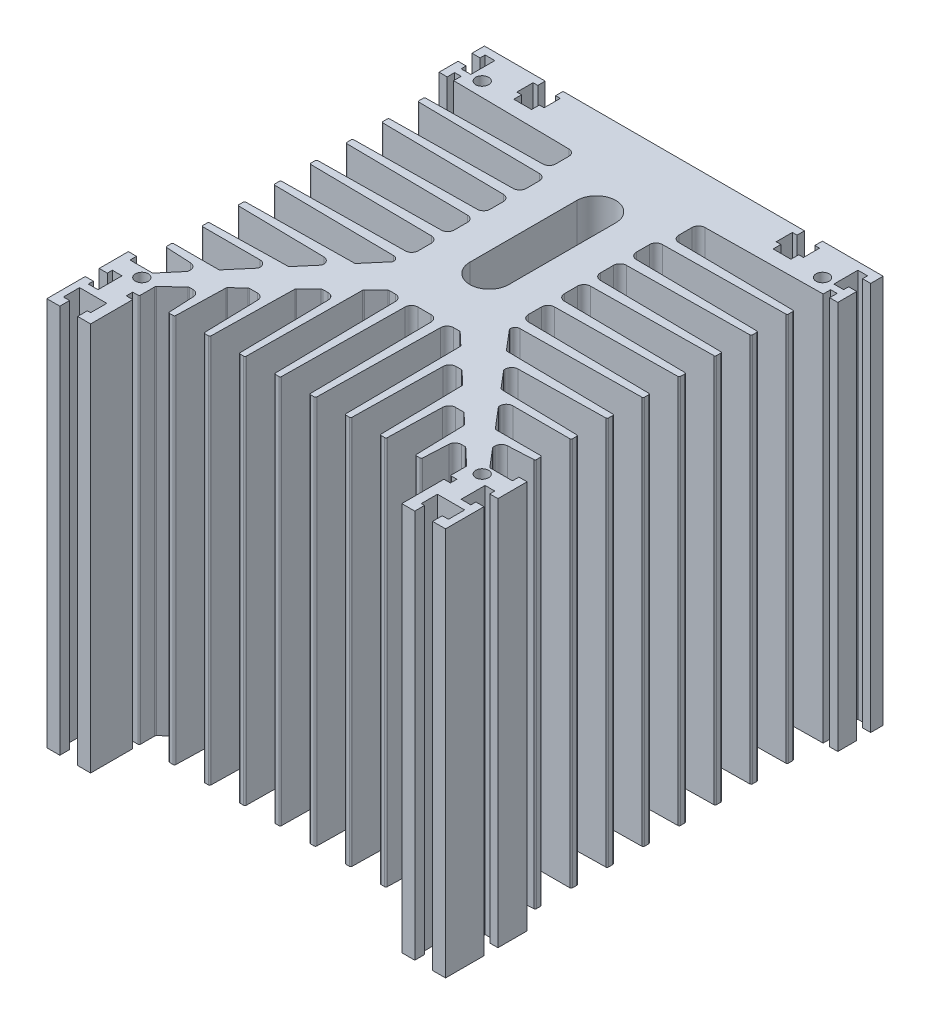
SolidWorks part; units mm, degrees
ref_plane "Alzado" through (0, 0, 0) normal (0, 0, 1) x (1, 0, 0)
ref_plane "Planta" through (0, 0, 0) normal (0, 1, 0) x (1, 0, 0)
ref_plane "Vista lateral" through (0, 0, 0) normal (1, 0, 0) x (0, 0, -1)
sketch "Croquis1" plane through (0, 0, 0) normal (0, 1, 0) x (1, 0, 0)
  line L0 (0, 0) -> (0, 30.5493) construction
  line L1 (-57.5, -11.85) -> (-57.5, -8.85)
  line L2 (-57.5, -8.85) -> (-59.4, -8.85)
  line L3 (-59.4, -8.85) -> (-59.4, -3.85)
  line L4 (-59.4, -3.85) -> (-51, -3.85)
  line L5 (-51, -3.85) -> (-51, -8.85)
  line L6 (-51, -8.85) -> (-52, -8.85)
  line L7 (-52, -8.85) -> (-52, -11.85)
  line L8 (-52, -11.85) -> (-48, -11.85)
  line L9 (-48, -11.85) -> (-48, 1.15)
  line L13 (-57.5, -11.85) -> (-61.5, -11.85)
  line L14 (-61.5, -11.85) -> (-61.5, 0)
  line L15 (-61.5, 0) -> (-59, 0)
  line L16 (-59, 0) -> (-59, -1.55)
  line L17 (-59, -1.55) -> (-56, -1.55)
  line L18 (-56, -1.55) -> (-56, 5.85)
  line L19 (-56, 5.85) -> (-59, 5.85)
  line L20 (-59, 5.85) -> (-59, 4.3)
  line L21 (-59, 4.3) -> (-61.5, 4.3)
  line L22 (-61.5, 4.3) -> (-61.5, 13.3)
  line L23 (-61.5, 13.3) -> (-59, 13.3)
  line L24 (-59, 13.3) -> (-59, 11.3)
  line L25 (-59, 11.3) -> (-57, 11.3)
  line L26 (-48, 1.15) -> (-50, 1.15)
  line L27 (-50, 1.15) -> (-50, 3.15)
  line L28 (-50, 3.15) -> (50, 3.15)
  line L29 (-61.5, 123.15) -> (-189.2921, 123.15) construction
  line L30 (-61.5, 123.15) -> (-61.5, 119.3)
  line L31 (-61.5, 119.3) -> (-59, 119.3)
  line L32 (-59, 119.3) -> (-59, 120.85)
  line L33 (-59, 120.85) -> (-56, 120.85)
  line L34 (-56, 120.85) -> (-56, 113.45)
  line L35 (-56, 113.45) -> (-59, 113.45)
  line L36 (-59, 113.45) -> (-59, 115)
  line L37 (-59, 115) -> (-61.5, 115)
  line L38 (-61.5, 115) -> (-61.5, 109.15)
  line L39 (-61.5, 109.15) -> (-59, 109.15)
  line L40 (-59, 109.15) -> (-59, 111.45)
  line L41 (-59, 111.45) -> (-57, 111.45)
  line L42 (-57, 111.45) -> (-57, 11.3)
  line L43 (37.25, 123.15) -> (-1, 123.15)
  line L44 (37.25, 120.85) -> (37.25, 123.15)
  line L45 (-61.5, 123.15) -> (-42.75, 123.15)
  line L46 (35.8, 120.85) -> (37.25, 120.85)
  line L47 (-42.75, 123.15) -> (-42.75, 120.85)
  line L48 (-42.75, 120.85) -> (-44.2, 120.85)
  line L49 (-44.2, 120.85) -> (-44.2, 115.85)
  line L50 (-44.2, 115.85) -> (-42.75, 115.85)
  line L51 (-42.75, 115.85) -> (-42.75, 113.45)
  line L52 (-42.75, 113.45) -> (-37.25, 113.45)
  line L53 (-37.25, 113.45) -> (-37.25, 115.85)
  line L54 (-37.25, 115.85) -> (-35.8, 115.85)
  line L55 (-35.8, 115.85) -> (-35.8, 120.85)
  line L56 (-35.8, 120.85) -> (-37.25, 120.85)
  line L57 (-37.25, 120.85) -> (-37.25, 123.15)
  line L58 (-37.25, 123.15) -> (1, 123.15)
  line L59 (35.8, 115.85) -> (35.8, 120.85)
  line L60 (37.25, 115.85) -> (35.8, 115.85)
  line L61 (37.25, 113.45) -> (37.25, 115.85)
  line L62 (42.75, 113.45) -> (37.25, 113.45)
  line L63 (42.75, 115.85) -> (42.75, 113.45)
  line L64 (44.2, 115.85) -> (42.75, 115.85)
  line L65 (44.2, 120.85) -> (44.2, 115.85)
  line L66 (42.75, 120.85) -> (44.2, 120.85)
  line L67 (42.75, 123.15) -> (42.75, 120.85)
  line L68 (61.5, 123.15) -> (42.75, 123.15)
  line L69 (57, 111.45) -> (57, 11.3)
  line L70 (59, 111.45) -> (57, 111.45)
  line L71 (59, 109.15) -> (59, 111.45)
  line L72 (61.5, 109.15) -> (59, 109.15)
  line L73 (61.5, 115) -> (61.5, 109.15)
  line L74 (59, 115) -> (61.5, 115)
  line L75 (59, 113.45) -> (59, 115)
  line L76 (56, 113.45) -> (59, 113.45)
  line L77 (56, 120.85) -> (56, 113.45)
  line L78 (59, 120.85) -> (56, 120.85)
  line L79 (59, 119.3) -> (59, 120.85)
  line L80 (61.5, 119.3) -> (59, 119.3)
  line L81 (61.5, 123.15) -> (61.5, 119.3)
  line L82 (50, 1.15) -> (50, 3.15)
  line L83 (48, 1.15) -> (50, 1.15)
  line L84 (59, 11.3) -> (57, 11.3)
  line L85 (59, 13.3) -> (59, 11.3)
  line L86 (61.5, 13.3) -> (59, 13.3)
  line L87 (61.5, 4.3) -> (61.5, 13.3)
  line L88 (59, 4.3) -> (61.5, 4.3)
  line L89 (59, 5.85) -> (59, 4.3)
  line L90 (56, 5.85) -> (59, 5.85)
  line L91 (56, -1.55) -> (56, 5.85)
  line L92 (59, -1.55) -> (56, -1.55)
  line L93 (59, 0) -> (59, -1.55)
  line L94 (61.5, 0) -> (59, 0)
  line L95 (61.5, -11.85) -> (61.5, 0)
  line L96 (57.5, -11.85) -> (61.5, -11.85)
  line L97 (48, -11.85) -> (48, 1.15)
  line L98 (52, -11.85) -> (48, -11.85)
  line L99 (52, -8.85) -> (52, -11.85)
  line L100 (51, -8.85) -> (52, -8.85)
  line L101 (51, -3.85) -> (51, -8.85)
  line L102 (59.4, -3.85) -> (51, -3.85)
  line L103 (59.4, -8.85) -> (59.4, -3.85)
  line L104 (57.5, -8.85) -> (59.4, -8.85)
  line L105 (57.5, -11.85) -> (57.5, -8.85)
  point P13 (-52, -10.35)
  point P62 (-37.25, 122)
  point P91 (0, 3.15)
  point P115 (-40, 113.45)
  dimension "D1" = 5.5
  dimension "D2" = 4
  dimension "D3" = 13
  dimension "D4" = 8.4
  dimension "D5" = 1
  dimension "D6" = 5
  dimension "D7" = 96
  dimension "D8" = 3
  dimension "D9" = 11.85
  dimension "D10" = 2.5
  dimension "D11" = 3
  dimension "D12" = 4.3
  dimension "D13" = 7.4
  dimension "D14" = 9
  dimension "D15" = 135
  dimension "D16" = 40
  dimension "D17" = 2
  dimension "D18" = 62.5
  dimension "D20" = 7.4
  dimension "D21" = 4.3
  dimension "D22" = 3.85
  dimension "D23" = 2.5
  dimension "D24" = 14
  dimension "D25" = 2
  dimension "D26" = 2
  dimension "D28" = 8.4
  dimension "D29" = 5.5
  dimension "D30" = 5
extrude "Saliente-Extruir1" add sketch "Croquis1" along normal blind 120 contours L105 L96 L95 L94 L93 L92 L91 L90 L89 L88 L87 L86 L85 L84 L69 L70 L71 L72 L73 L74 L75 L76 L77 L78 L79 L80 L81 L68 L67 L66 L65 L64 L63 L62 L61 L60 L59 L46 L44 L43 L58 L57 L56 L55 L54 L53 L52 L51 L50 L49
sketch "Croquis2" plane through (0, 120, 0) normal (0, 1, 0) x (1, 0, 0)
  line L0 (0, 3.15) -> (0, 43.15) construction
  line L1 (-50, 3.15) -> (50, 3.15) construction
  line L2 (-2.0248, 43.15) -> (2.0248, 43.15)
  line L3 (-48, 3.15) -> (-48, 8.15)
  line L4 (-48, -11.85) -> (-48, 1.15) construction
  line L5 (-11, 43.15) -> (11, 43.15) construction
  line L6 (-48, 8.15) -> (-11, 43.15) construction
  line L7 (48, 8.15) -> (11, 43.15) construction
  line L8 (48, 3.15) -> (48, 7.9347)
  line L9 (-4.5, 3.15) -> (4.5, 3.15)
  line L10 (-4.0247, 41.175) -> (-4.5, 3.15)
  line L11 (4.0247, 41.175) -> (4.5, 3.15)
  line L12 (6.375, 3.15) -> (15.375, 3.15)
  line L13 (10.875, 3.15) -> (11, 43.15) construction
  line L15 (6.9692, 41.1812) -> (6.375, 3.15)
  line L16 (15.0375, 39.1201) -> (15.375, 3.15)
  line L17 (11.1446, 43.0132) -> (14.8812, 39.4786)
  line L18 (8.969, 43.15) -> (10.801, 43.15)
  line L19 (17.25, 3.15) -> (26.25, 3.15)
  line L20 (21.75, 3.15) -> (21.75, 33.15) construction
  line L21 (21.3724, 33.15) -> (19.7169, 33.15)
  line L22 (17.7172, 31.1833) -> (17.25, 3.15)
  line L24 (25.7845, 28.9584) -> (26.25, 3.15)
  line L25 (21.716, 33.0132) -> (25.6281, 29.3126)
  line L26 (28.125, 3.15) -> (37.125, 3.15)
  line L27 (48, 3.15) -> (39, 3.15)
  line L28 (32.625, 3.15) -> (32.625, 22.15) construction
  line L29 (32.625, 22.15) -> (30.5731, 22.15)
  line L30 (28.5738, 20.2026) -> (28.125, 3.15)
  line L31 (32.625, 22.15) -> (33.001, 22.15)
  line L32 (36.7179, 18.62) -> (37.125, 3.15)
  line L33 (33.3446, 22.0132) -> (36.5617, 18.97)
  line L34 (43.5, 3.15) -> (43.5, 13.15) construction
  line L35 (42.5153, 13.15) -> (41.4025, 13.15)
  line L36 (39, 3.15) -> (39.405, 11.2499)
  line L37 (42.8589, 13.0132) -> (47.8436, 8.2979)
  line L38 (-43.5, 3.15) -> (-43.5, 13.15) construction
  line L39 (-32.625, 3.15) -> (-32.625, 22.15) construction
  line L40 (-21.75, 3.15) -> (-21.75, 33.15) construction
  line L41 (-10.875, 3.15) -> (-11, 43.15) construction
  line L42 (-48, 8.15) -> (-11, 43.15) construction
  line L43 (-42.8589, 13.0132) -> (-47.8436, 8.2979)
  line L44 (-39, 3.15) -> (-39.405, 11.2499)
  line L45 (-42.5153, 13.15) -> (-41.4025, 13.15)
  line L46 (-33.3446, 22.0132) -> (-36.5617, 18.97)
  line L47 (-36.7179, 18.62) -> (-37.125, 3.15)
  line L48 (-32.625, 22.15) -> (-33.001, 22.15)
  line L49 (-28.5738, 20.2026) -> (-28.125, 3.15)
  line L50 (-32.625, 22.15) -> (-30.5731, 22.15)
  line L51 (-48, 3.15) -> (-39, 3.15)
  line L52 (-28.125, 3.15) -> (-37.125, 3.15)
  line L53 (-21.716, 33.0132) -> (-25.6281, 29.3126)
  line L54 (-25.7845, 28.9584) -> (-26.25, 3.15)
  line L55 (-17.7172, 31.1833) -> (-17.25, 3.15)
  line L56 (-21.3724, 33.15) -> (-19.7169, 33.15)
  line L57 (-17.25, 3.15) -> (-26.25, 3.15)
  line L58 (-8.969, 43.15) -> (-10.801, 43.15)
  line L59 (-11.1446, 43.0132) -> (-14.8812, 39.4786)
  line L60 (-15.0375, 39.1201) -> (-15.375, 3.15)
  line L61 (-6.9692, 41.1812) -> (-6.375, 3.15)
  line L62 (-6.375, 3.15) -> (-15.375, 3.15)
  line L63 (-48, 3.15) -> (-48, 7.9347)
  arc A0 (41.4025, 13.15) -> (39.405, 11.2499) centre (41.4025, 11.15) ccw
  arc A1 (30.5731, 22.15) -> (28.5738, 20.2026) centre (30.5731, 20.15) ccw
  arc A2 (19.7169, 33.15) -> (17.7172, 31.1833) centre (19.7169, 31.15) ccw
  arc A3 (8.969, 43.15) -> (6.9692, 41.1812) centre (8.969, 41.15) ccw
  arc A4 (2.0248, 43.15) -> (4.0247, 41.175) centre (2.0248, 41.15) cw
  arc A5 (-2.0248, 43.15) -> (-4.0247, 41.175) centre (-2.0248, 41.15) ccw
  arc A6 (47.8436, 8.2979) -> (48, 7.9347) centre (47.5, 7.9347) cw
  arc A7 (42.8589, 13.0132) -> (42.5153, 13.15) centre (42.5153, 12.65) ccw
  arc A8 (36.5617, 18.97) -> (36.7179, 18.62) centre (36.2181, 18.6068) cw
  arc A9 (33.3446, 22.0132) -> (33.001, 22.15) centre (33.001, 21.65) ccw
  arc A10 (25.6281, 29.3126) -> (25.7845, 28.9584) centre (25.2845, 28.9493) cw
  arc A11 (21.716, 33.0132) -> (21.3724, 33.15) centre (21.3724, 32.65) ccw
  arc A12 (14.8812, 39.4786) -> (15.0375, 39.1201) centre (14.5376, 39.1154) cw
  arc A13 (11.1446, 43.0132) -> (10.801, 43.15) centre (10.801, 42.65) ccw
  arc A14 (-11.1446, 43.0132) -> (-10.801, 43.15) centre (-10.801, 42.65) cw
  arc A15 (-14.8812, 39.4786) -> (-15.0375, 39.1201) centre (-14.5376, 39.1154) ccw
  arc A16 (-21.716, 33.0132) -> (-21.3724, 33.15) centre (-21.3724, 32.65) cw
  arc A17 (-25.6281, 29.3126) -> (-25.7845, 28.9584) centre (-25.2845, 28.9493) ccw
  arc A18 (-33.3446, 22.0132) -> (-33.001, 22.15) centre (-33.001, 21.65) cw
  arc A19 (-36.5617, 18.97) -> (-36.7179, 18.62) centre (-36.2181, 18.6068) ccw
  arc A20 (-42.8589, 13.0132) -> (-42.5153, 13.15) centre (-42.5153, 12.65) cw
  arc A21 (-47.8436, 8.2979) -> (-48, 7.9347) centre (-47.5, 7.9347) ccw
  arc A22 (-8.969, 43.15) -> (-6.9692, 41.1812) centre (-8.969, 41.15) cw
  arc A23 (-19.7169, 33.15) -> (-17.7172, 31.1833) centre (-19.7169, 31.15) cw
  arc A24 (-30.5731, 22.15) -> (-28.5738, 20.2026) centre (-30.5731, 20.15) cw
  arc A25 (-41.4025, 13.15) -> (-39.405, 11.2499) centre (-41.4025, 11.15) cw
  point P8 (0, 43.15)
  point P14 (0, 43.15)
  point P20 (0, 3.15)
  point P26 (11, 43.15)
  point P30 (21.75, 3.15)
  point P48 (39.5, 13.15)
  point P51 (28.625, 22.15)
  point P54 (17.75, 33.15)
  point P57 (7, 43.15)
  point P60 (4, 43.15)
  point P63 (-4, 43.15)
  point P69 (42.7143, 13.15)
  point P72 (36.7124, 18.8274)
  point P75 (33.2, 22.15)
  point P78 (25.7807, 29.1683)
  point P81 (21.5714, 33.15)
  point P84 (15.0355, 39.3326)
  point P138 (-15.0355, 39.3326)
  point P139 (-21.5714, 33.15)
  point P140 (-25.7807, 29.1683)
  point P141 (-33.2, 22.15)
  point P142 (-36.7124, 18.8274)
  point P143 (-42.7143, 13.15)
  point P144 (-7, 43.15)
  point P145 (-17.75, 33.15)
  point P146 (-28.625, 22.15)
  point P147 (-39.5, 13.15)
  dimension "D24" = 2
  dimension "D25" = 0.5
  dimension "D1" = 40
  dimension "D2" = 8
  dimension "D3" = 5
  dimension "D4" = 22
  dimension "D5" = 9
  dimension "D6" = 1.875
  dimension "D7" = 9
  dimension "D8" = 7.9994
  dimension "D9" = 4
  dimension "D10" = 1.875
  dimension "D11" = 30
  dimension "D12" = 4
  dimension "D13" = 8.0959
  dimension "D14" = 9
  dimension "D15" = 1.875
  dimension "D16" = 9
  dimension "D17" = 19
  dimension "D18" = 4
  dimension "D19" = 8.0874
  dimension "D20" = 8
  dimension "D21" = 10
  dimension "D22" = 4
  dimension "D23" = 4
extrude "Cortar-Extruir1" cut sketch "Croquis2" against normal blind 120 contours A25 L45 A20 L43 A21 L3 L51 L44 | A24 L50 L48 A18 L46 A19 L47 L52 L49 | A23 L56 A16 L53 A17 L54 L57 L55 | A22 L58 A14 L59 A15 L60 L62 L61 | L2 A5 L10 L9 L11 A4 | L17 A13 L18 A3 L15 L12 L16 A12 | L25 A11 L21 A2 L22 L19 L24 A10 | L33 A9 L31 L29 A1 L30 L26 L32 A8 | L37 A7 L35 A0 L36 L27 L8 A6
fillet "Redondeo1" radius 0.4 18 edges at (48, 60, -3.15) (-48, 60, -3.15) (39, 60, -3.15) (37.125, 60, -3.15) (28.125, 60, -3.15) (26.25, 60, -3.15) (17.25, 60, -3.15) (15.375, 60, -3.15) (6.375, 60, -3.15) (4.5, 60, -3.15) (-4.5, 60, -3.15) (-6.375, 60, -3.15) (-15.375, 60, -3.15) (-17.25, 60, -3.15) (-26.25, 60, -3.15) (-28.125, 60, -3.15) (-37.125, 60, -3.15) (-39, 60, -3.15)
sketch "Croquis3" plane through (0, 120, 0) normal (0, 1, 0) x (1, 0, 0)
  line L0 (-57, 109.15) -> (-19, 109.15) construction
  line L1 (-57, 111.45) -> (-57, 11.3) construction
  line L2 (-61.5, 109.15) -> (-59, 109.15) construction
  line L3 (-57, 109.15) -> (-57, 100.15)
  line L4 (-57, 104.65) -> (-19, 104.65) construction
  line L5 (-19, 102.6239) -> (-19, 106.6761)
  line L6 (-57, 109.15) -> (-20.9737, 108.676)
  line L7 (-57, 100.15) -> (-20.9737, 100.624)
  line L8 (-57, 98.0438) -> (-57, 89.0438)
  line L9 (-57, 93.5438) -> (-17, 93.5438) construction
  line L10 (-17, 91.5189) -> (-17, 95.5686)
  line L11 (-57, 98.0438) -> (-18.975, 97.5684)
  line L12 (-57, 89.0438) -> (-18.975, 89.5191)
  line L13 (-57, 86.9375) -> (-57, 77.9375)
  line L14 (-57, 82.4375) -> (-17, 82.4375) construction
  line L15 (-17, 80.4127) -> (-17, 84.4623)
  line L16 (-18.975, 86.4622) -> (-57, 86.9375)
  line L17 (-57, 77.9375) -> (-18.975, 78.4128)
  line L18 (-57, 75.8313) -> (-57, 66.8313)
  line L19 (-57, 71.3313) -> (-17, 71.3313) construction
  line L20 (-17, 69.3064) -> (-17, 73.3561)
  line L21 (-57, 75.8313) -> (-18.975, 75.3559)
  line L22 (-57, 66.8313) -> (-18.975, 67.3066)
  line L23 (-57, 64.725) -> (-57, 55.725)
  line L24 (-57, 60.225) -> (-17, 60.225) construction
  line L25 (-17, 58.2002) -> (-17, 62.2498)
  line L26 (-18.975, 64.2497) -> (-57, 64.725)
  line L27 (-57, 55.725) -> (-18.975, 56.2003)
  line L28 (-57, 11.3) -> (-52.2315, 11.3)
  line L29 (-17, 97.5438) -> (-17, 52.5438) construction
  line L30 (-56, 117.15) -> (-61.4392, 117.15) construction
  line L31 (-57, 31.4063) -> (-57, 22.4063)
  line L32 (-56, 120.85) -> (-56, 113.45) construction
  line L33 (-56, 2.15) -> (-61.4392, 2.15) construction
  line L34 (-57, 26.9063) -> (-37, 26.9063) construction
  line L35 (-37, 29.1595) -> (-37, 29.4063)
  line L36 (-57, 31.4063) -> (-39, 31.4063)
  line L37 (-56, -1.55) -> (-56, 5.85) construction
  line L38 (-57, 53.6188) -> (-57, 44.6188)
  line L39 (-57, 49.1188) -> (-18, 49.1188) construction
  line L40 (-18, 51.5489) -> (-18, 51.6379)
  line L41 (-57, 53.6188) -> (-19.4808, 53.1377)
  line L42 (-17, 52.5438) -> (-52, 11.3) construction
  line L44 (-23.5556, 45.0833) -> (-57, 44.6188)
  line L45 (-18.1188, 51.2254) -> (-23.1814, 45.2597)
  line L46 (-57, 42.5125) -> (-57, 33.5125)
  line L47 (-57, 38.0125) -> (-29.3314, 38.0125) construction
  line L48 (-28, 39.765) -> (-28, 40.0467)
  line L49 (-29.9655, 42.0464) -> (-57, 42.5125)
  line L51 (-57, 33.5125) -> (-32.9511, 34.0079)
  line L52 (-28.1188, 39.4415) -> (-32.5801, 34.1842)
  line L53 (-57, 22.4063) -> (-42.8066, 22.4063)
  line L54 (-42.4253, 22.5827) -> (-37.1188, 28.8359)
  line L55 (-57, 11.3) -> (-57, 20.3)
  line L56 (-57, 15.8) -> (-47, 15.8) construction
  line L57 (-57, 20.3) -> (-48.9001, 19.895)
  line L58 (-47, 17.8975) -> (-47, 17.3755)
  line L59 (-51.8502, 11.4765) -> (-47.1188, 17.052)
  line L60 (0, 0) -> (0, 43.15) construction
  line L61 (-2.0248, 43.15) -> (2.0248, 43.15) construction
  line L62 (57, 15.8) -> (47, 15.8) construction
  line L63 (57, 38.0125) -> (29.3314, 38.0125) construction
  line L64 (17, 52.5438) -> (52, 11.3) construction
  line L65 (57, 49.1188) -> (18, 49.1188) construction
  line L66 (57, 26.9063) -> (37, 26.9063) construction
  line L67 (56, 2.15) -> (61.4392, 2.15) construction
  line L68 (56, 117.15) -> (61.4392, 117.15) construction
  line L69 (17, 97.5438) -> (17, 52.5438) construction
  line L70 (57, 60.225) -> (17, 60.225) construction
  line L71 (57, 71.3313) -> (17, 71.3313) construction
  line L72 (57, 82.4375) -> (17, 82.4375) construction
  line L73 (57, 93.5438) -> (17, 93.5438) construction
  line L74 (57, 104.65) -> (19, 104.65) construction
  line L75 (57, 109.15) -> (19, 109.15) construction
  line L76 (51.8502, 11.4765) -> (47.1188, 17.052)
  line L77 (47, 17.8975) -> (47, 17.3755)
  line L78 (57, 20.3) -> (48.9001, 19.895)
  line L79 (57, 11.3) -> (57, 20.3)
  line L80 (42.4253, 22.5827) -> (37.1188, 28.8359)
  line L81 (57, 22.4063) -> (42.8066, 22.4063)
  line L82 (28.1188, 39.4415) -> (32.5801, 34.1842)
  line L83 (57, 33.5125) -> (32.9511, 34.0079)
  line L84 (29.9655, 42.0464) -> (57, 42.5125)
  line L85 (28, 39.765) -> (28, 40.0467)
  line L86 (57, 42.5125) -> (57, 33.5125)
  line L87 (18.1188, 51.2254) -> (23.1814, 45.2597)
  line L88 (23.5556, 45.0833) -> (57, 44.6188)
  line L89 (57, 53.6188) -> (19.4808, 53.1377)
  line L90 (18, 51.5489) -> (18, 51.6379)
  line L91 (57, 53.6188) -> (57, 44.6188)
  line L92 (57, 31.4063) -> (39, 31.4063)
  line L93 (37, 29.1595) -> (37, 29.4063)
  line L94 (57, 31.4063) -> (57, 22.4063)
  line L95 (57, 11.3) -> (52.2315, 11.3)
  line L96 (57, 55.725) -> (18.975, 56.2003)
  line L97 (18.975, 64.2497) -> (57, 64.725)
  line L98 (17, 58.2002) -> (17, 62.2498)
  line L99 (57, 64.725) -> (57, 55.725)
  line L100 (57, 66.8313) -> (18.975, 67.3066)
  line L101 (57, 75.8313) -> (18.975, 75.3559)
  line L102 (17, 69.3064) -> (17, 73.3561)
  line L103 (57, 75.8313) -> (57, 66.8313)
  line L104 (57, 77.9375) -> (18.975, 78.4128)
  line L105 (18.975, 86.4622) -> (57, 86.9375)
  line L106 (17, 80.4127) -> (17, 84.4623)
  line L107 (57, 86.9375) -> (57, 77.9375)
  line L108 (57, 89.0438) -> (18.975, 89.5191)
  line L109 (57, 98.0438) -> (18.975, 97.5684)
  line L110 (17, 91.5189) -> (17, 95.5686)
  line L111 (57, 98.0438) -> (57, 89.0438)
  line L112 (57, 100.15) -> (20.9737, 100.624)
  line L113 (57, 109.15) -> (20.9737, 108.676)
  line L114 (19, 102.6239) -> (19, 106.6761)
  line L115 (57, 109.15) -> (57, 100.15)
  arc A0 (-28, 40.0467) -> (-29.9655, 42.0464) centre (-30, 40.0467) ccw
  arc A1 (-17, 58.2002) -> (-18.975, 56.2003) centre (-19, 58.2002) cw
  arc A2 (-17, 62.2498) -> (-18.975, 64.2497) centre (-19, 62.2498) ccw
  arc A3 (-17, 69.3064) -> (-18.975, 67.3066) centre (-19, 69.3064) cw
  arc A4 (-17, 73.3561) -> (-18.975, 75.3559) centre (-19, 73.3561) ccw
  arc A5 (-17, 80.4127) -> (-18.975, 78.4128) centre (-19, 80.4127) cw
  arc A6 (-17, 84.4623) -> (-18.975, 86.4622) centre (-19, 84.4623) ccw
  arc A7 (-17, 91.5189) -> (-18.975, 89.5191) centre (-19, 91.5189) cw
  arc A8 (-17, 95.5686) -> (-18.975, 97.5684) centre (-19, 95.5686) ccw
  arc A9 (-19, 102.6239) -> (-20.9737, 100.624) centre (-21, 102.6239) cw
  arc A10 (-19, 106.6761) -> (-20.9737, 108.676) centre (-21, 106.6761) ccw
  arc A11 (-37, 29.4063) -> (-39, 31.4063) centre (-39, 29.4063) ccw
  arc A12 (-48.9001, 19.895) -> (-47, 17.8975) centre (-49, 17.8975) cw
  arc A13 (-18, 51.6379) -> (-19.4808, 53.1377) centre (-19.5, 51.6379) ccw
  arc A14 (-52.2315, 11.3) -> (-51.8502, 11.4765) centre (-52.2315, 11.8) ccw
  arc A15 (-47.1188, 17.052) -> (-47, 17.3755) centre (-47.5, 17.3755) ccw
  arc A16 (-42.4253, 22.5827) -> (-42.8066, 22.4063) centre (-42.8066, 22.9063) cw
  arc A17 (-37.1188, 28.8359) -> (-37, 29.1595) centre (-37.5, 29.1595) ccw
  arc A18 (-28.1188, 39.4415) -> (-28, 39.765) centre (-28.5, 39.765) ccw
  arc A19 (-32.5801, 34.1842) -> (-32.9511, 34.0079) centre (-32.9614, 34.5078) cw
  arc A20 (-18.1188, 51.2254) -> (-18, 51.5489) centre (-18.5, 51.5489) ccw
  arc A21 (-23.1814, 45.2597) -> (-23.5556, 45.0833) centre (-23.5626, 45.5832) cw
  arc A22 (23.1814, 45.2597) -> (23.5556, 45.0833) centre (23.5626, 45.5832) ccw
  arc A23 (18.1188, 51.2254) -> (18, 51.5489) centre (18.5, 51.5489) cw
  arc A24 (32.5801, 34.1842) -> (32.9511, 34.0079) centre (32.9614, 34.5078) ccw
  arc A25 (28.1188, 39.4415) -> (28, 39.765) centre (28.5, 39.765) cw
  arc A26 (37.1188, 28.8359) -> (37, 29.1595) centre (37.5, 29.1595) cw
  arc A27 (42.4253, 22.5827) -> (42.8066, 22.4063) centre (42.8066, 22.9063) ccw
  arc A28 (47.1188, 17.052) -> (47, 17.3755) centre (47.5, 17.3755) cw
  arc A29 (52.2315, 11.3) -> (51.8502, 11.4765) centre (52.2315, 11.8) cw
  arc A30 (18, 51.6379) -> (19.4808, 53.1377) centre (19.5, 51.6379) cw
  arc A31 (48.9001, 19.895) -> (47, 17.8975) centre (49, 17.8975) ccw
  arc A32 (37, 29.4063) -> (39, 31.4063) centre (39, 29.4063) cw
  arc A33 (19, 106.6761) -> (20.9737, 108.676) centre (21, 106.6761) cw
  arc A34 (19, 102.6239) -> (20.9737, 100.624) centre (21, 102.6239) ccw
  arc A35 (17, 95.5686) -> (18.975, 97.5684) centre (19, 95.5686) cw
  arc A36 (17, 91.5189) -> (18.975, 89.5191) centre (19, 91.5189) ccw
  arc A37 (17, 84.4623) -> (18.975, 86.4622) centre (19, 84.4623) cw
  arc A38 (17, 80.4127) -> (18.975, 78.4128) centre (19, 80.4127) ccw
  arc A39 (17, 73.3561) -> (18.975, 75.3559) centre (19, 73.3561) cw
  arc A40 (17, 69.3064) -> (18.975, 67.3066) centre (19, 69.3064) ccw
  arc A41 (17, 62.2498) -> (18.975, 64.2497) centre (19, 62.2498) cw
  arc A42 (17, 58.2002) -> (18.975, 56.2003) centre (19, 58.2002) ccw
  arc A43 (28, 40.0467) -> (29.9655, 42.0464) centre (30, 40.0467) cw
  point P12 (-19, 104.65)
  point P19 (-17, 93.5438)
  point P26 (-17, 82.4375)
  point P33 (-17, 71.3313)
  point P40 (-17, 60.225)
  point P73 (-37, 26.9063)
  point P81 (-28, 42.0125)
  point P88 (-17, 67.3313)
  point P93 (-17, 78.4375)
  point P98 (-17, 89.5438)
  point P104 (-19, 100.65)
  point P107 (-19, 108.65)
  point P112 (-47, 19.8)
  point P115 (-18, 53.1188)
  point P121 (-47, 17.192)
  point P124 (-42.5751, 22.4063)
  point P129 (-28, 39.5814)
  point P132 (-32.7259, 34.0125)
  point P135 (-18, 51.3654)
  point P138 (-23.3284, 45.0864)
  point P254 (23.3284, 45.0864)
  point P255 (18, 51.3654)
  point P256 (32.7259, 34.0125)
  point P257 (28, 39.5814)
  point P258 (42.5751, 22.4063)
  point P259 (47, 17.192)
  point P260 (18, 53.1188)
  point P261 (47, 19.8)
  point P262 (19, 108.65)
  point P263 (19, 100.65)
  point P264 (17, 89.5438)
  point P265 (17, 78.4375)
  point P266 (17, 67.3313)
  point P267 (28, 42.0125)
  dimension "D30" = 2
  dimension "D31" = 2
  dimension "D32" = 2
  dimension "D33" = 1.5
  dimension "D34" = 0.5
  dimension "D1" = 38
  dimension "D2" = 9
  dimension "D3" = 8
  dimension "D4" = 2.1063
  dimension "D5" = 9
  dimension "D6" = 40
  dimension "D7" = 8
  dimension "D8" = 2.1063
  dimension "D9" = 9
  dimension "D10" = 2.1063
  dimension "D11" = 9
  dimension "D12" = 2.1063
  dimension "D13" = 5
  dimension "D14" = 2.1063
  dimension "D15" = 39
  dimension "D16" = 4
  dimension "D17" = 45
  dimension "D18" = 8.0323
  dimension "D19" = 2.1063
  dimension "D20" = 4
  dimension "D21" = 2.4311
  dimension "D22" = 4
  dimension "D23" = 2.1063
  dimension "D24" = 20
  dimension "D25" = 9
  dimension "D26" = 1.7534
  dimension "D27" = 10
  dimension "D28" = 4
  dimension "D29" = 2.608
extrude "Cortar-Extruir2" cut sketch "Croquis3" against normal through all
sketch "Croquis4" plane through (0, 120, 0) normal (0, 1, 0) x (1, 0, 0)
  line L0 (0, 43.15) -> (0, 123.15) construction
  line L1 (-2.0248, 43.15) -> (2.0248, 43.15) construction
  line L2 (37.25, 123.15) -> (-37.25, 123.15) construction
  line L3 (0, 96.15) -> (0, 63.15) construction
  line L4 (6, 96.15) -> (6, 63.15)
  line L5 (-6, 96.15) -> (-6, 63.15)
  arc A0 (6, 96.15) -> (-6, 96.15) centre (0, 96.15) ccw
  arc A1 (-6, 63.15) -> (6, 63.15) centre (0, 63.15) ccw
  point P8 (0, 79.65)
  dimension "D1" = 45
  dimension "D3" = 21
  dimension "D2" = 12
extrude "Cortar-Extruir3" cut sketch "Croquis4" against normal through all
fillet "Redondeo2" radius 0.4 32 edges at (57, 60, -100.15) (57, 60, -98.0438) (57, 60, -89.0438) (57, 60, -86.9375) (57, 60, -77.9375) (57, 60, -75.8313) (57, 60, -66.8313) (57, 60, -64.725) (57, 60, -55.725) (57, 60, -53.6188) (57, 60, -44.6188) (57, 60, -42.5125) (57, 60, -33.5125) (57, 60, -31.4063) (57, 60, -22.4063) (57, 60, -20.3) (-57, 60, -20.3) (-57, 60, -22.4063) (-57, 60, -31.4063) (-57, 60, -33.5125) (-57, 60, -42.5125) (-57, 60, -44.6188) (-57, 60, -53.6188) (-57, 60, -55.725) (-57, 60, -66.8313) (-57, 60, -64.725) (-57, 60, -75.8313) (-57, 60, -77.9375) (-57, 60, -86.9375) (-57, 60, -89.0438) (-57, 60, -98.0438) (-57, 60, -100.15)
sketch "Croquis5" plane through (0, 120, 0) normal (0, 1, 0) x (1, 0, 0)
  line L0 (-56, 113.45) -> (-59, 113.45) construction
  line L1 (0, 0) -> (0, 11.1372) construction
  circle A0 centre (-52.5, 8.45) radius 2
  circle A1 centre (-52.5, 113.45) radius 2
  circle A2 centre (52.5, 113.45) radius 2
  circle A3 centre (52.5, 8.45) radius 2
  dimension "D2" = 4
  dimension "D1" = 52.5
  dimension "D3" = 105
extrude "Cortar-Extruir4" cut sketch "Croquis5" against normal blind 10
